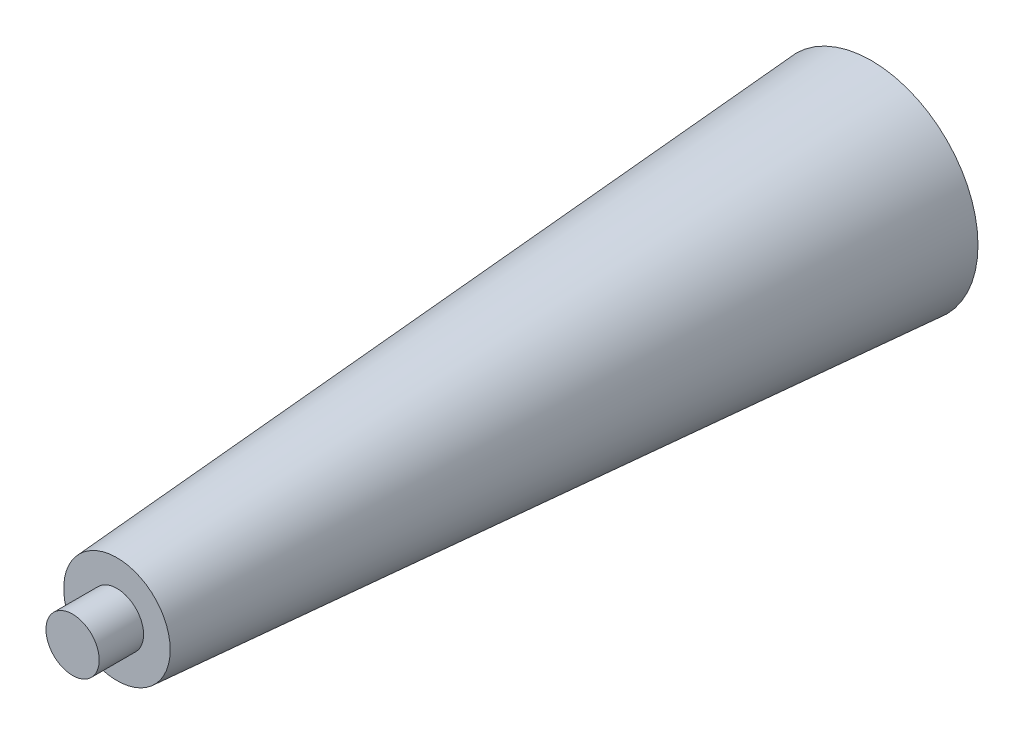
SolidWorks part; units mm, degrees
material "PF"
ref_plane "Ön Düzlem" through (0, 0, 0) normal (0, 0, 1) x (1, 0, 0)
ref_plane "Üst Düzlem" through (0, 0, 0) normal (0, 1, 0) x (1, 0, 0)
ref_plane "Sağ Düzlem" through (0, 0, 0) normal (1, 0, 0) x (0, 0, -1)
sketch "Çizim2" plane through (0, 0, 0) normal (0, 1, 0) x (1, 0, 0)
  line L0 (0, 0) -> (12, 0)
  line L2 (0, -85) -> (0, 0)
  line L3 (0, -85) -> (6, -85)
  line L4 (6, -85) -> (12, 0)
  dimension "D1" = 85
  dimension "D2" = 12
  dimension "D3" = 6
ref_axis "Eksen1" through (0, 0, 89.25) along (0, 0, -1)
revolve "Döndür1" add sketch "Çizim2" angle 360 about axis through (0, 0, 89.25) along (0, 0, -1)
sketch "Çizim3" plane through (0, 0, 85) normal (0, 0, 1) x (1, 0, 0)
  circle A0 centre (0, 0) radius 3
  dimension "D1" = 6
extrude "Yükseklik-Ekstrüzyon1" add sketch "Çizim3" along normal blind 5
ref_point "Nokta1"
